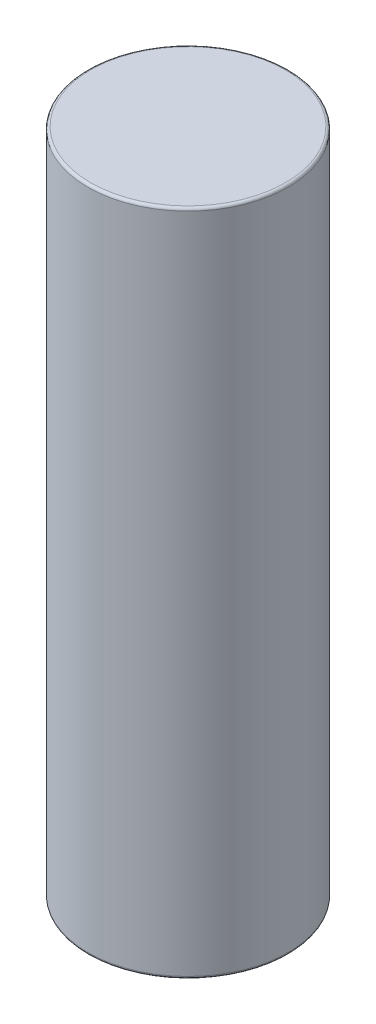
SolidWorks part; units mm, degrees
ref_plane "Front Plane" through (0, 0, 0) normal (0, 0, 1) x (1, 0, 0)
ref_plane "Top Plane" through (0, 0, 0) normal (0, 1, 0) x (1, 0, 0)
ref_plane "Right Plane" through (0, 0, 0) normal (1, 0, 0) x (0, 0, -1)
sketch "Sketch1" plane through (0, 0, 0) normal (0, 1, 0) x (1, 0, 0)
  circle A0 centre (0, 0) radius 15
  dimension "D1" = 30
extrude "Boss-Extrude1" add sketch "Sketch1" along normal blind 100
fillet "Fillet1" radius 0.4 2 edges at (0, 0, 15) (0, 100, 15)
